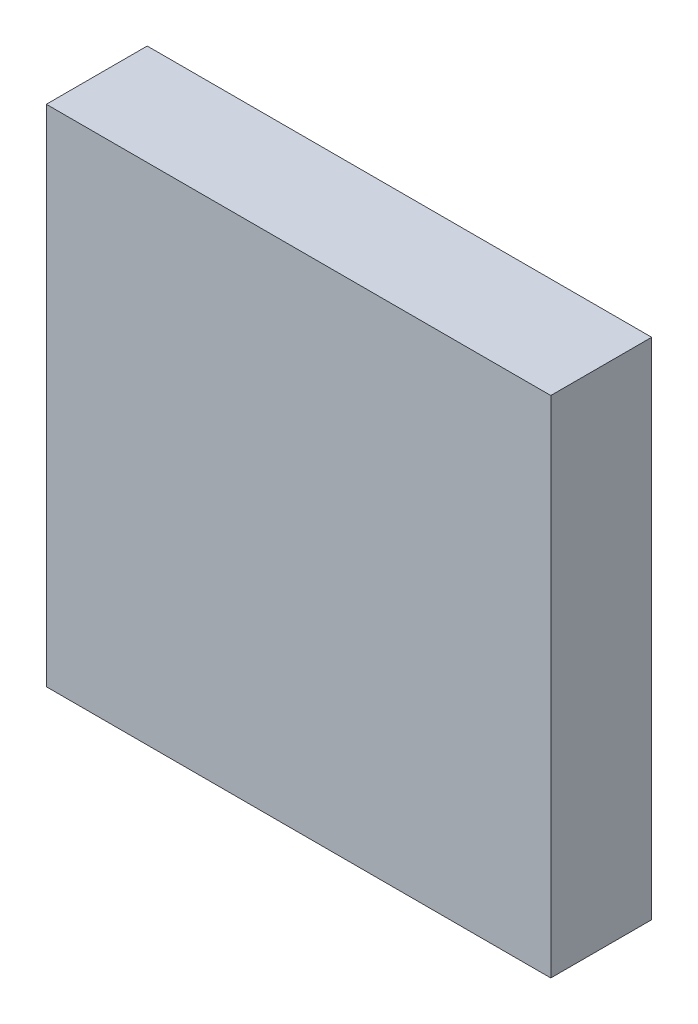
SolidWorks part; units mm, degrees
ref_plane "Front Plane" through (0, 0, 0) normal (1, 0, 0) x (0, 1, 0)
ref_plane "Top Plane" through (0, 0, 0) normal (0, 0, 1) x (0, 1, 0)
ref_plane "Right Plane" through (0, 0, 0) normal (0, 1, 0) x (-1, 0, 0)
sketch "Sketch1" plane through (0, 0, 0) normal (0, 0, 1) x (0, 1, 0)
  line L1 (12.5, 12.5) -> (-12.5, 12.5)
  line L2 (12.5, 12.5) -> (12.5, -12.5)
  line L3 (12.5, -12.5) -> (-12.5, -12.5)
  line L4 (-12.5, 12.5) -> (-12.5, -12.5)
  line L5 (12.5, 12.5) -> (-12.5, -12.5) construction
  line L6 (12.5, -12.5) -> (-12.5, 12.5) construction
  point P0 (0, 0)
  dimension "D1" = 25
  dimension "D2" = 25
extrude "Boss-Extrude1" add sketch "Sketch1" along normal blind 5
